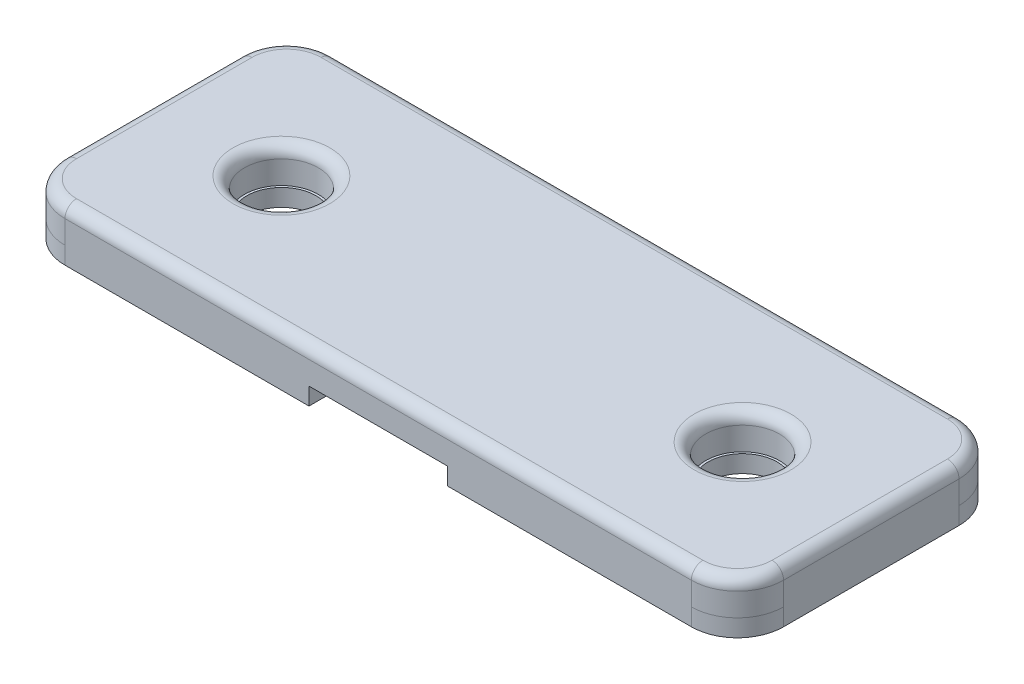
SolidWorks part; units mm, degrees
ref_plane "Front Plane" through (0, 0, 0) normal (0, 0, 1) x (1, 0, 0)
ref_plane "Top Plane" through (0, 0, 0) normal (0, 1, 0) x (1, 0, 0)
ref_plane "Right Plane" through (0, 0, 0) normal (1, 0, 0) x (0, 0, -1)
sketch "Sketch1" plane through (0, 0, 0) normal (0, 1, 0) x (1, 0, 0)
  line L0 (0, 0) -> (10, 0) construction
  line L1 (0, 0) -> (-10, 0) construction
  line L3 (15.5834, -5.8044) -> (-15.5834, -5.8044)
  line L4 (15.5834, -5.8044) -> (15.5834, 5.8044)
  line L5 (15.5834, 5.8044) -> (-15.5834, 5.8044)
  line L6 (-15.5834, -5.8044) -> (-15.5834, 5.8044)
  line L7 (15.5834, -5.8044) -> (-15.5834, 5.8044) construction
  line L8 (15.5834, 5.8044) -> (-15.5834, -5.8044) construction
  circle A0 centre (-10, 0) radius 1.6
  circle A1 centre (10, 0) radius 1.6
extrude "Boss-Extrude1" add sketch "Sketch1" along normal blind 1.5
fillet "Fillet1" radius 2 4 edges at (-15.5834, 0.75, -5.8044) (15.5834, 0.75, -5.8044) (15.5834, 0.75, 5.8044) (-15.5834, 0.75, 5.8044)
ref_plane "Plane1" through (0, 0, 0) normal (0, -1, 0) x (-1, 0, 0)
sketch "Sketch2" plane through (0, 0, 0) normal (0, -1, 0) x (-1, 0, 0)
  line L0 (0, 0) -> (-3, 0) construction
  line L1 (0, 0) -> (3, 0) construction
  line L2 (15.5834, 0.2529) -> (15.5834, -9.6434) construction
  line L5 (15.5834, 3.8044) -> (15.5834, -3.8044) construction
  line L6 (0, -5.8044) -> (17.7863, -5.8044) construction
  line L7 (13.5834, -5.8044) -> (-13.5834, -5.8044) construction
  line L8 (0, 5.8044) -> (17.7863, 5.8044) construction
  line L9 (-13.5834, 5.8044) -> (13.5834, 5.8044) construction
  line L10 (0, -5.8044) -> (-23.4732, -5.8044) construction
  line L11 (3, -5.8044) -> (15.5834, -5.8044)
  line L12 (3, -5.8044) -> (3, 5.8044)
  line L13 (3, 5.8044) -> (15.5834, 5.8044)
  line L14 (15.5834, -5.8044) -> (15.5834, 5.8044)
  line L15 (0, 5.8044) -> (-25.3334, 5.8044) construction
  line L16 (-15.5834, 0) -> (-15.5834, 12.7908) construction
  line L17 (-15.5834, -3.8044) -> (-15.5834, 3.8044) construction
  line L19 (-3, -5.8044) -> (-15.5834, -5.8044)
  line L20 (-3, -5.8044) -> (-3, 5.8044)
  line L21 (-3, 5.8044) -> (-15.5834, 5.8044)
  line L22 (-15.5834, -5.8044) -> (-15.5834, 5.8044)
  circle A0 centre (10, 0) radius 1.5
  circle A2 centre (-10, 0) radius 1.5
extrude "Boss-Extrude2" add sketch "Sketch2" along normal blind 0.75
fillet "Fillet2" radius 2 4 edges at (-15.5834, -0.375, 5.8044) (-15.5834, -0.375, -5.8044) (15.5834, -0.375, 5.8044) (15.5834, -0.375, -5.8044)
fillet "Fillet3" radius 0.5 10 edges at (10, 1.5, 1.6) (14.9976, 1.5, -5.2186) (15.5834, 1.5, 0) (14.9976, 1.5, 5.2186) (0, 1.5, 5.8044) (-14.9976, 1.5, 5.2186) (-15.5834, 1.5, 0) (-14.9976, 1.5, -5.2186) (0, 1.5, -5.8044) (-10, 1.5, 1.6)
